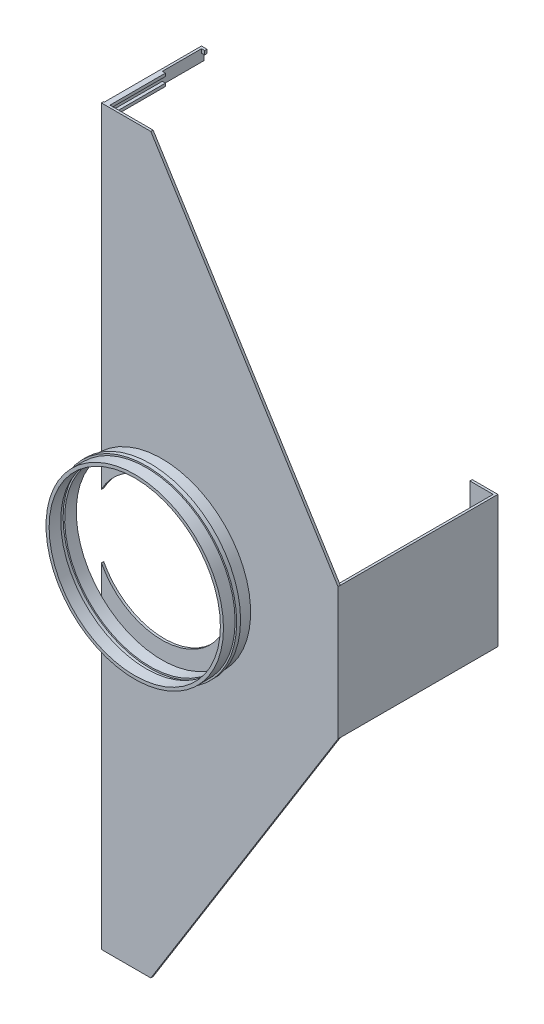
SolidWorks part; units mm, degrees
material "6063-T4"
ref_plane "Front Plane" through (0, 0, 0) normal (0, 0, 1) x (1, 0, 0)
ref_plane "Top Plane" through (0, 0, 0) normal (0, 1, 0) x (1, 0, 0)
ref_plane "Right Plane" through (0, 0, 0) normal (1, 0, 0) x (0, 0, -1)
sketch "Sketch1" plane through (0, 0, 0) normal (0, 0, 1) x (1, 0, 0)
  line L0 (0, 0) -> (101.6, 0) construction
  line L1 (305, 0) -> (305, 1058.8625) construction
  line L2 (0, 0) -> (305, 0)
  line L3 (305, 0) -> (305, 945)
  line L4 (305, 945) -> (0, 945)
  line L5 (0, 945) -> (0, 0)
  point P0 (0, 0)
  point P4 (305, 0)
  point P7 (305, 945)
  dimension "D1" = 305
  dimension "D2" = 945
extrude "Extrude1" add sketch "Sketch1" along normal blind 3
sketch "Sketch2" plane through (0, 0, 3) normal (0, 0, 1) x (1, 0, 0)
  line L0 (0, 945) -> (0, 0) construction
  line L1 (0, 472.5) -> (680.2815, 472.5) construction
  circle A0 centre (78, 472.5) radius 110.37
  circle A1 centre (78, 472.5) radius 114.37
  point P0 (0, 472.5)
  point P5 (78, 472.5)
  dimension "D2" = 228.74
  dimension "D3" = 220.74
  dimension "D1" = 78
extrude "Extrude2" add sketch "Sketch2" along normal blind 15
sketch "Sketch3" plane through (0, 0, 0) normal (0, 0, -1) x (-1, 0, 0)
  line L0 (-305, 945) -> (0, 945) construction
  line L1 (-1, 945) -> (-1, -154.374) construction
  line L2 (0, 0) -> (-305, 0) construction
  line L3 (-4, 945) -> (-4, -154.374) construction
  line L4 (-1, 930) -> (-33.6212, 930) construction
  line L5 (-1, 15) -> (-109.5759, 15) construction
  line L6 (-1, 945) -> (-1, 930)
  line L7 (-1, 930) -> (-4, 930)
  line L8 (-4, 930) -> (-4, 945)
  line L9 (-4, 945) -> (-1, 945)
  line L10 (-1, 0) -> (-1, 15)
  line L11 (-1, 15) -> (-4, 15)
  line L12 (-4, 15) -> (-4, 0)
  line L13 (-4, 0) -> (-1, 0)
  line L15 (-27.3164, 945) -> (-27.3164, 909.2694) construction
  point P0 (0, 945)
  point P1 (0, 0)
  point P3 (-1, 945)
  point P9 (-1, 0)
  point P10 (-4, 945)
  point P15 (-1, 930)
  point P18 (-4, 930)
  point P19 (-1, 15)
  point P22 (-4, 15)
  point P23 (-4, 0)
  point P26 (-27.3164, 945)
  point P31 (-27.3164, 941.2099)
  point P32 (-27.3164, 933.4105)
  dimension "D1" = 1
  dimension "D2" = 3
  dimension "D3" = 15
  dimension "FROM_TOP" = 15
extrude "Extrude3" add sketch "Sketch3" along normal blind 125
sketch "Sketch4" plane through (4, 0, 0) normal (1, 0, 0) x (0, 0, -1)
  line L0 (125, 945) -> (0, 945) construction
  line L1 (125, 945) -> (125, 930) construction
  line L2 (125, 940) -> (64.468, 940) construction
  line L3 (122, 945) -> (122, 875.8093) construction
  line L4 (125, 945) -> (125, 940)
  line L5 (125, 940) -> (122, 940)
  line L6 (122, 940) -> (122, 945)
  line L7 (122, 945) -> (125, 945)
  line L8 (125, 0) -> (0, 0) construction
  line L9 (125, 15) -> (125, 0) construction
  line L10 (125, 6) -> (76.2668, 6) construction
  line L11 (122, 0) -> (122, 19.05) construction
  line L12 (125, 0) -> (125, 6)
  line L13 (125, 6) -> (122, 6)
  line L14 (122, 6) -> (122, 0)
  line L15 (122, 0) -> (125, 0)
  line L16 (-3, 945) -> (71.4375, 945)
  line L17 (71.4375, 945) -> (71.4375, 941.1735)
  line L18 (71.4375, 941.1735) -> (-3, 941.1735)
  line L19 (-3, 0) -> (-3, 945) construction
  line L20 (-3, 941.1735) -> (-3, 945)
  line L21 (71.4375, 930) -> (71.4375, 933.7986)
  line L22 (125, 930) -> (0, 930) construction
  line L23 (71.4375, 933.7986) -> (-3, 933.7986)
  line L24 (-3, 933.7986) -> (-3, 930)
  line L25 (-3, 930) -> (71.4375, 930)
  line L26 (-3, 0) -> (52.3875, 0)
  line L27 (52.3875, 0) -> (52.3875, 4.7625)
  line L28 (52.3875, 4.7625) -> (-3, 4.7625)
  line L29 (-3, 4.7625) -> (-3, 0)
  line L30 (52.3875, 15) -> (-3, 15)
  line L32 (125, 15) -> (0, 15) construction
  line L33 (-3, 15) -> (-3, 11.1125)
  line L34 (-3, 11.1125) -> (52.3875, 11.1125)
  line L35 (52.3875, 11.1125) -> (52.3875, 15)
  point P0 (125, 945)
  point P1 (122, 945)
  point P3 (125, 940)
  point P12 (122, 940)
  point P14 (125, 0)
  point P16 (122, 0)
  point P18 (125, 6)
  point P27 (122, 6)
  dimension "D1" = 3
  dimension "D2" = 5
  dimension "D3" = 3
  dimension "D4" = 6
extrude "Extrude4" add sketch "Sketch4" along normal blind 4
sketch "Sketch5" plane through (0, 0, 0) normal (0, 0, -1) x (-1, 0, 0)
  line L0 (-305, 0) -> (-305, 945) construction
  line L1 (-305, 387.5) -> (-176.9375, 387.5) construction
  line L2 (-302, 387.5) -> (-302, 612.478) construction
  line L3 (-305, 557.5) -> (-242.2846, 557.5) construction
  line L4 (-305, 557.5) -> (-302, 557.5)
  line L5 (-302, 557.5) -> (-302, 387.5)
  line L6 (-302, 387.5) -> (-305, 387.5)
  line L7 (-305, 387.5) -> (-305, 557.5)
  point P0 (-305, 472.5)
  point P1 (-305, 557.5)
  point P4 (-305, 387.5)
  point P7 (-302, 387.5)
  point P12 (-302, 557.5)
  dimension "D1" = 85
  dimension "SIDE" = 85
  dimension "D2" = 3
extrude "Extrude5" add sketch "Sketch5" along normal blind 203
sketch "Sketch6" plane through (302, 0, 0) normal (-1, 0, 0) x (0, 0, 1)
  line L0 (-203, 387.5) -> (0, 387.5) construction
  line L1 (-200, 387.5) -> (-200, 576.0411) construction
  line L2 (-203, 557.5) -> (0, 557.5) construction
  line L3 (-203, 387.5) -> (-200, 387.5)
  line L4 (-200, 387.5) -> (-200, 557.5)
  line L5 (-200, 557.5) -> (-203, 557.5)
  line L6 (-203, 557.5) -> (-203, 387.5)
  point P0 (-203, 557.5)
  point P1 (-203, 387.5)
  point P3 (-200, 387.5)
  point P9 (-200, 557.5)
  dimension "D1" = 3
extrude "Extrude6" add sketch "Sketch6" along normal blind 30
sketch "Sketch7" plane through (0, 0, 0) normal (0, 0, -1) x (-1, 0, 0)
  line L0 (-305, 945) -> (-8, 945) construction
  line L1 (-305, 557.5) -> (-63.7149, 945)
  line L2 (-63.7149, 945) -> (-305, 945)
  line L3 (-305, 945) -> (-305, 557.5)
  line L4 (-63.7149, 945) -> (-63.7149, -381.1455) construction
  line L5 (-305, 387.5) -> (-63.7149, 0)
  line L6 (-63.7149, 0) -> (-305, 0)
  line L7 (-305, 0) -> (-305, 387.5)
  point P0 (-305, 557.5)
  point P1 (-63.7149, 945)
  point P7 (-305, 387.5)
  point P10 (-63.7149, 0)
extrude "Extrude7" cut sketch "Sketch7" against normal through all
sketch "Sketch13" plane through (0, 0, 3) normal (0, 0, 1) x (1, 0, 0)
  circle A0 centre (78, 472.5) radius 88.0987
  point P0 (78, 472.5)
extrude "Extrude10" cut sketch "Sketch13" against normal through all
sketch "Sketch22" plane through (0, 0, 18) normal (0, 0, 1) x (1, 0, 0)
  circle A0 centre (78, 472.5) radius 116.4
  circle A1 centre (78, 472.5) radius 112.37
  point P0 (78, 472.5)
extrude "Extrude17" add sketch "Sketch22" along normal blind 5
sketch "Sketch23" plane through (0, 0, 23) normal (0, 0, 1) x (1, 0, 0)
  circle A0 centre (78, 472.5) radius 114.37
  circle A1 centre (78, 472.5) radius 110.37
  point P0 (78, 472.5)
extrude "Extrude18" add sketch "Sketch23" along normal blind 15
sketch "Sketch19" plane through (0, 0, 3) normal (0, 0, 1) x (1, 0, 0)
  line L0 (78, 472.5) -> (78, 1020.274)
  line L1 (78, 1020.274) -> (395.2875, 484.1875)
  line L2 (395.2875, 484.1875) -> (395.2875, 82.55)
  line L3 (78, 472.5) -> (78, -48.2576)
  line L4 (78, -48.2576) -> (395.2875, 82.55)
  point P0 (78, 472.5)
extrude "Extrude16" [suppressed] cut sketch "Sketch19" against normal through all and the other way through all
equation "\"D3@Sketch3\" = \"FROM_TOP\""
equation "\"D1@Sketch5\" = \"SIDE\""
